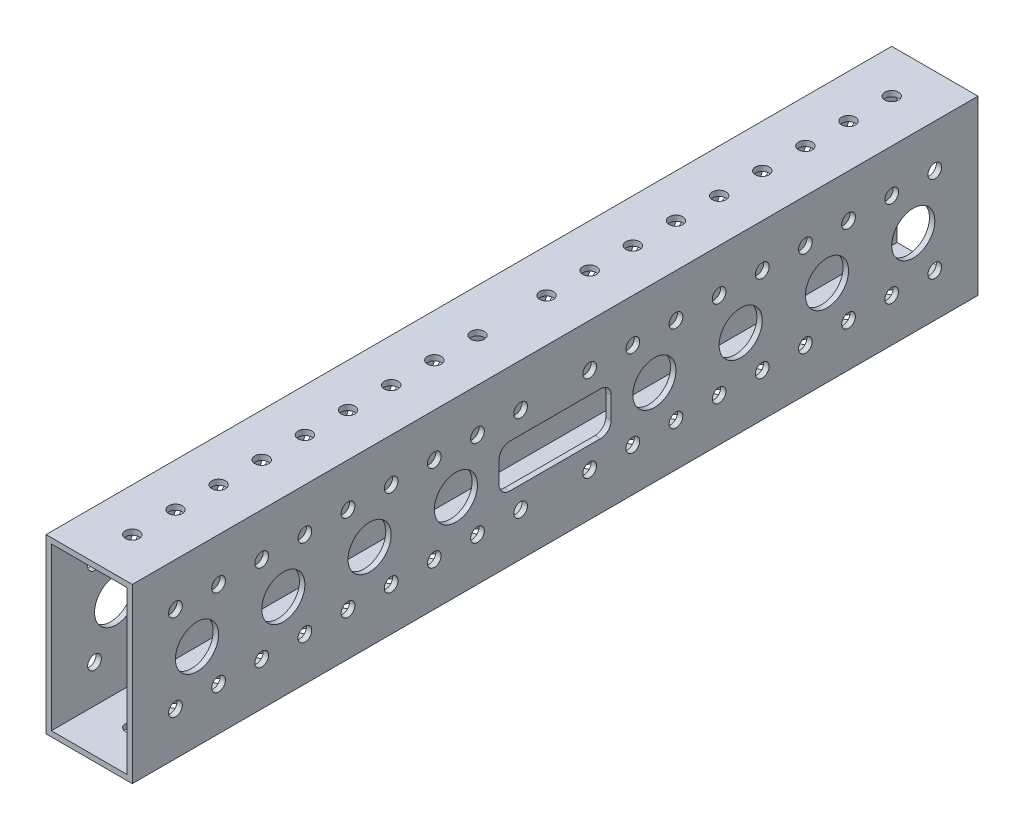
SolidWorks part; units mm, degrees
material "6061 Alloy"
ref_plane "Front Plane" through (0, 0, 0) normal (0, 0, 1) x (1, 0, 0)
ref_plane "Top Plane" through (0, 0, 0) normal (0, 1, 0) x (1, 0, 0)
ref_plane "Right Plane" through (0, 0, 0) normal (1, 0, 0) x (0, 0, -1)
sketch "Sketch1" plane through (0, 0, 0) normal (0, 0, 1) x (1, 0, 0)
  line L1 (0, 0) -> (25.4, 0)
  line L2 (0, 0) -> (0, 50.8)
  line L3 (0, 50.8) -> (25.4, 50.8)
  line L4 (25.4, 0) -> (25.4, 50.8)
  dimension "D1" = 25.4
  dimension "D2" = 50.8
extrude "Boss-Extrude1" add sketch "Sketch1" along normal blind 248.92
shell "Shell1" thickness 1.5875
sketch "Sketch8" plane through (25.4, 0, 0) normal (1, 0, 0) x (0, 0, -1)
  line L0 (-124.46, 101.6) -> (-124.46, 0) construction
  line L2 (-248.92, 0) -> (0, 0) construction
  line L4 (-248.92, 0) -> (-248.92, 50.8) construction
  line L5 (0, 0) -> (0, 50.8) construction
hole_wizard "#21 (0.159) Diameter Hole1" positions "Sketch2" profile "Sketch3" hole size "#21" standard "ANSI Inch" end condition through all
sketch "Sketch2" plane through (0, 50.8, 0) normal (0, 1, 0) x (1, 0, 0)
  line L0 (25.4, -248.92) -> (25.4, 0) construction
  line L1 (25.4, -248.92) -> (0, -248.92) construction
  point P0 (12.7, -236.22)
  dimension "D1" = 12.7
  dimension "D2" = 12.7
sketch "Sketch3" plane through (12.7, 50.8, 236.22) normal (1, 0, 0) x (0, 0, 1)
  line L0 (0, 0) -> (0, 50.8)
  line L1 (0, 50.8) -> (2.0193, 50.8)
  line L2 (2.0193, 50.8) -> (2.0193, 0)
  line L5 (2.0193, 0) -> (0, 0)
  line L11 (0, -6.35) -> (0, 107.95) construction
  dimension "Thru Hole Dia." = 4.0386
  dimension "Thru Hole Depth" = 50.8
pattern_linear "LPattern1" count 9 spacing 12.7 along (0, 0, -1) of "#21 (0.159) Diameter Hole1"
hole_wizard "#21 (0.159) Diameter Hole2" positions "Sketch4" profile "Sketch5" hole size "#21" standard "ANSI Inch" end condition through all
sketch "Sketch4" plane through (25.4, 0, 0) normal (1, 0, 0) x (0, 0, -1)
  line L0 (-248.92, 50.8) -> (0, 50.8) construction
  line L1 (-248.92, 0) -> (-248.92, 50.8) construction
  point P0 (-236.22, 38.1)
  dimension "D1" = 12.7
  dimension "D2" = 12.7
sketch "Sketch5" plane through (25.4, 38.1, 236.22) normal (0, 1, 0) x (0, 0, -1)
  line L0 (0, 0) -> (0, 25.4)
  line L1 (0, 25.4) -> (2.0193, 25.4)
  line L2 (2.0193, 25.4) -> (2.0193, 0)
  line L5 (2.0193, 0) -> (0, 0)
  line L11 (0, -6.35) -> (0, 107.95) construction
  dimension "Thru Hole Dia." = 4.0386
  dimension "Thru Hole Depth" = 25.4
pattern_linear "LPattern2" count 9 spacing 12.7 along (0, 0, -1) count 2 spacing 25.4 along (0, -1, 0) of "#21 (0.159) Diameter Hole2"
hole_wizard "1/2 (0.5) Diameter Hole1" positions "Sketch6" profile "Sketch7" hole size "1/2" standard "ANSI Inch" end condition through all
sketch "Sketch6" plane through (25.4, 0, 0) normal (1, 0, 0) x (0, 0, -1)
  line L0 (-248.92, 50.8) -> (0, 50.8) construction
  line L1 (-248.92, 0) -> (-248.92, 50.8) construction
  point P0 (-229.87, 25.4)
  dimension "D1" = 25.4
  dimension "D2" = 19.05
sketch "Sketch7" plane through (25.4, 25.4, 229.87) normal (0, 1, 0) x (0, 0, -1)
  line L0 (0, 0) -> (0, 25.4)
  line L1 (0, 25.4) -> (6.35, 25.4)
  line L2 (6.35, 25.4) -> (6.35, 0)
  line L5 (6.35, 0) -> (0, 0)
  line L11 (0, -6.35) -> (0, 107.95) construction
  dimension "Thru Hole Dia." = 12.7
  dimension "Thru Hole Depth" = 25.4
pattern_linear "LPattern3" count 4 spacing 25.4 along (0, 0, -1) of "1/2 (0.5) Diameter Hole1"
ref_plane "Plane1" through (0, 0, 124.46) normal (0, 0, 1) x (1, 0, 0)
mirror "Mirror1" about plane through (0, 0, 124.46) normal (0, 0, 1) of "LPattern3", "1/2 (0.5) Diameter Hole1", "LPattern2", "#21 (0.159) Diameter Hole2", "LPattern1", "#21 (0.159) Diameter Hole1"
sketch "Sketch9" plane through (25.4, 0, 0) normal (1, 0, 0) x (0, 0, -1)
  line L1 (-140.97, 31.75) -> (-107.95, 31.75)
  line L2 (-140.97, 31.75) -> (-140.97, 19.05)
  line L3 (-140.97, 19.05) -> (-107.95, 19.05)
  line L4 (-107.95, 31.75) -> (-107.95, 19.05)
  line L6 (-140.97, 31.75) -> (-107.95, 19.05) construction
  line L7 (-107.95, 31.75) -> (-140.97, 19.05) construction
  line L8 (-248.92, 50.8) -> (0, 50.8) construction
  line L11 (-124.46, 13.97) -> (-124.46, -13.97) construction
  point P4 (-124.46, 25.4)
  dimension "D1" = 25.4
  dimension "D2" = 12.7
  dimension "D3" = 33.02
extrude "Cut-Extrude1" cut sketch "Sketch9" against normal through all both and the other way through all contours L1 L4 L3 L2
fillet "Fillet1" radius 3.175 8 edges at (0.7937, 19.05, 140.97) (0.7937, 31.75, 140.97) (0.7937, 19.05, 107.95) (0.7937, 31.75, 107.95) (24.6062, 31.75, 107.95) (24.6062, 19.05, 107.95) (24.6062, 19.05, 140.97) (24.6062, 31.75, 140.97)
equation "\"length\"= \"D1@Boss-Extrude1\""
equation "\"even\"= 2 * ( int ( \"length\" / 2 ) )"
equation "\"cutout\"= \"length\" - \"even\" - 0.5"
equation "\"D3@Sketch9\"=\"cutout\""
